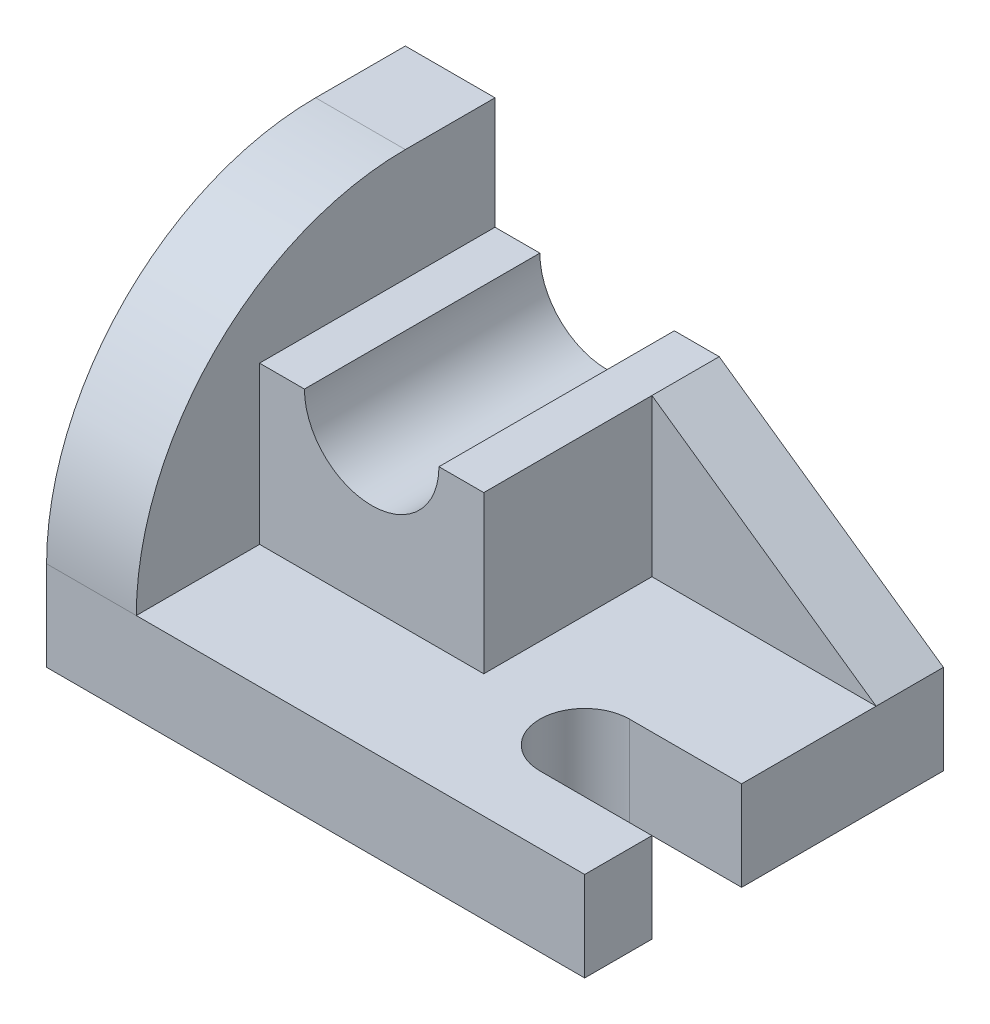
SolidWorks part; units mm, degrees
ref_plane "Front Plane" through (0, 0, 0) normal (0, 0, 1) x (1, 0, 0)
ref_plane "Top Plane" through (0, 0, 0) normal (0, 1, 0) x (1, 0, 0)
ref_plane "Right Plane" through (0, 0, 0) normal (1, 0, 0) x (0, 0, -1)
sketch "Sketch2" plane through (0, 0, 0) normal (0, 1, 0) x (1, 0, 0)
  line L0 (48, -12) -> (28, -12) construction
  line L1 (-48, -32) -> (48, -32)
  line L2 (-48, -32) -> (-48, 32)
  line L3 (-48, 32) -> (48, 32)
  line L4 (48, -32) -> (48, 32)
  line L5 (-48, -32) -> (48, 32) construction
  line L6 (-48, 32) -> (48, -32) construction
  line L7 (28, -12) -> (48, -12) construction
  line L8 (28, -4) -> (48, -4)
  line L9 (28, -20) -> (48, -20)
  line L10 (48, -4) -> (48, -20)
  arc A0 (28, -4) -> (28, -20) centre (28, -12) ccw
  point P0 (0, 0)
  point P8 (38, -12)
  dimension "D3" = 8
  dimension "D1" = 64
  dimension "D2" = 96
  dimension "D4" = 20
  dimension "D5" = 20
extrude "Boss-Extrude2" add sketch "Sketch2" along normal mid plane 16 contours A0 L8 L4 L3 L2 L1 L9
sketch "Sketch3" plane through (-48, 0, 0) normal (-1, 0, 0) x (0, 0, 1)
  line L0 (-16, 8) -> (32, 8)
  line L1 (-32, 8) -> (-16, 8)
  line L2 (-32, 8) -> (-32, 56)
  line L3 (-32, 56) -> (-16, 56)
  arc A0 (32, 8) -> (-16, 56) centre (-16, 8) ccw
  dimension "D2" = 48
  dimension "D1" = 16
extrude "Boss-Extrude3" add sketch "Sketch3" against normal blind 16
sketch "Sketch4" plane through (0, 0, -32) normal (0, 0, -1) x (-1, 0, 0)
  line L0 (0, 36) -> (24, 36)
  line L1 (32, 8) -> (-8, 8)
  line L2 (32, 8) -> (32, 36)
  line L3 (32, 36) -> (-8, 36)
  line L4 (-8, 8) -> (-8, 36)
  arc A0 (0, 36) -> (24, 36) centre (12, 36) ccw
  line M6 (32, 56) -> (32, 8)
  line M7 (32, 8) -> (-48, 8)
  dimension "D3" = 24
  dimension "D1" = 40
  dimension "D2" = 28
extrude "Boss-Extrude4" add sketch "Sketch4" against normal blind 42 contours A0 L3 L4 M7 M6
sketch "Sketch5" plane through (0, 0, -32) normal (0, 0, -1) x (-1, 0, 0)
  line L0 (-8, 36) -> (-48, 8)
  line L1 (-48, 8) -> (-8, 8)
  line L2 (-8, 8) -> (-8, 36) construction
  line L3 (-8, 8) -> (-48, 8) construction
  line L4 (-8, 8) -> (-8, 36)
extrude "Boss-Extrude5" add sketch "Sketch5" against normal blind 12
